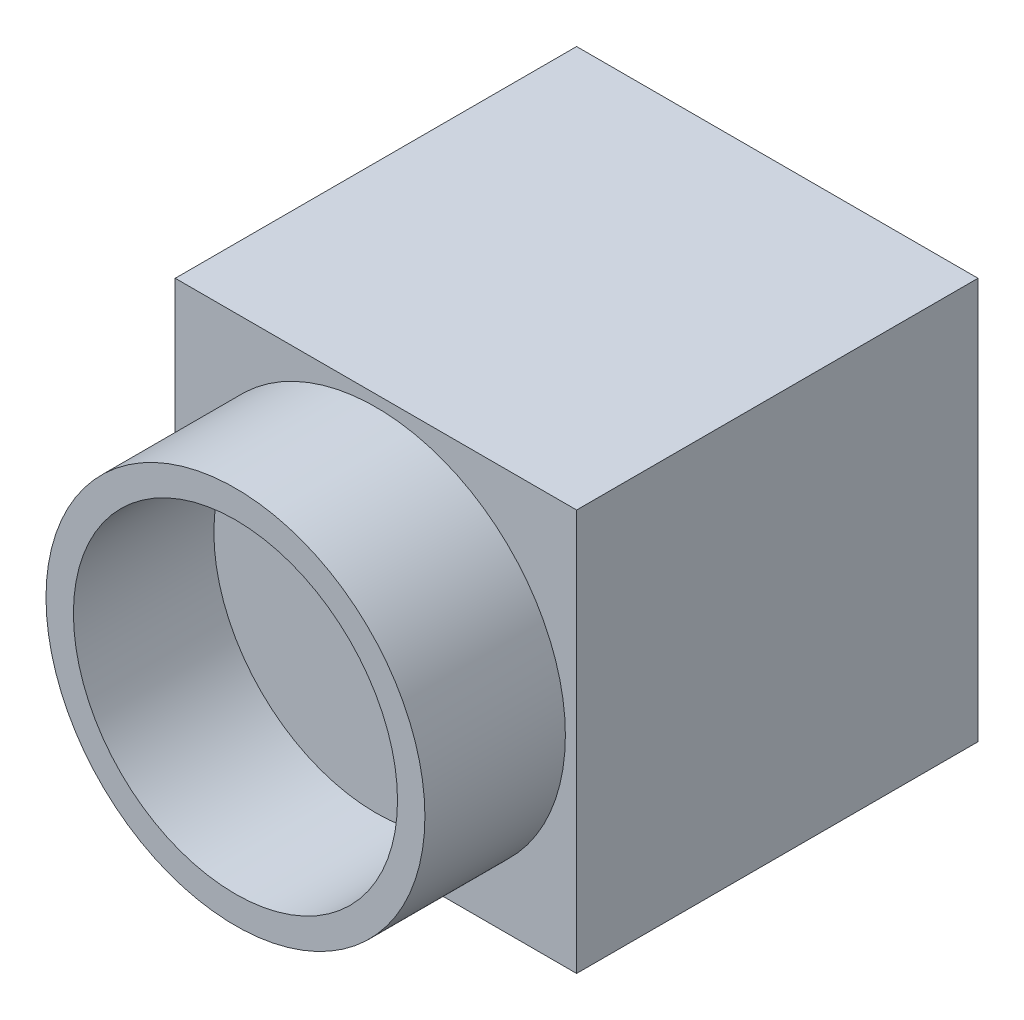
SolidWorks part; units mm, degrees
ref_plane "Front Plane" through (0, 0, 0) normal (0, 0, 1) x (1, 0, 0)
ref_plane "Top Plane" through (0, 0, 0) normal (0, 1, 0) x (1, 0, 0)
ref_plane "Right Plane" through (0, 0, 0) normal (1, 0, 0) x (0, 0, -1)
sketch "Sketch2" plane through (0, 0, 0) normal (0, 1, 0) x (1, 0, 0)
  line L1 (-14.645, 14.645) -> (14.645, 14.645)
  line L2 (-14.645, 14.645) -> (-14.645, -14.645)
  line L3 (-14.645, -14.645) -> (14.645, -14.645)
  line L4 (14.645, 14.645) -> (14.645, -14.645)
  line L5 (-14.645, 14.645) -> (14.645, -14.645) construction
  line L6 (-14.645, -14.645) -> (14.645, 14.645) construction
  point P0 (0, 0)
  dimension "D1" = 29.29
extrude "Boss-Extrude1" add sketch "Sketch2" along normal mid plane 29.29
sketch "Sketch3" plane through (0, 0, 14.645) normal (0, 0, 1) x (1, 0, 0)
  circle A0 centre (0, 0) radius 13.825
  dimension "D1" = 27.65
extrude "Boss-Extrude2" add sketch "Sketch3" along normal blind 10.25
sketch "Sketch4" plane through (0, 0, 24.895) normal (0, 0, 1) x (1, 0, 0)
  circle A0 centre (0, 0) radius 11.825
  circle A1 centre (0, 0) radius 13.825 construction
  dimension "D1" = 2
extrude "Cut-Extrude1" cut sketch "Sketch4" against normal up to surface (10.25 mm away) up to face at (13.825, 0, 14.645)
